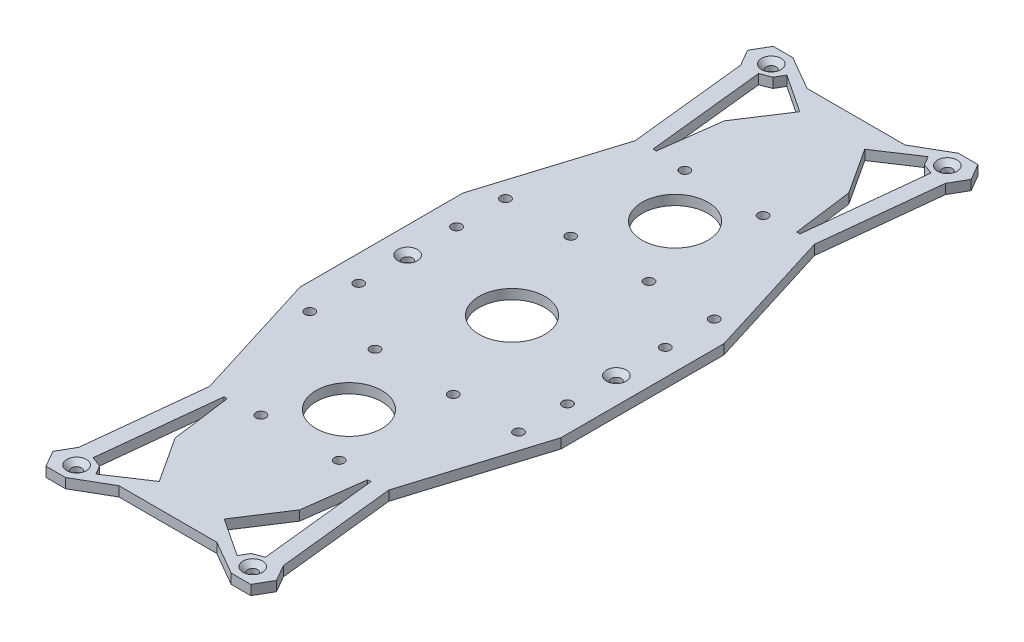
SolidWorks part; units mm, degrees
ref_plane "前视基准面" through (0, 0, 0) normal (0, 0, 1) x (1, 0, 0)
ref_plane "上视基准面" through (0, 0, 0) normal (0, 1, 0) x (1, 0, 0)
ref_plane "右视基准面" through (0, 0, 0) normal (1, 0, 0) x (0, 0, -1)
sketch "草图1" plane through (0, 0, 0) normal (0, 1, 0) x (1, 0, 0)
  line L0 (0, 0) -> (0, 105.5) construction
  line L1 (-15, 105.5) -> (15, 105.5)
  line L2 (-40, 25) -> (40, 25)
  line L3 (15, 105.5) -> (40, 25)
  line L4 (40, 25) -> (40, -25)
  line L5 (-40, 25) -> (-40, -25)
  line L6 (-15, 105.5) -> (-40, 25)
  line L7 (-40, 0) -> (49960, 0) construction
  line L8 (-15, -105.5) -> (15, -105.5)
  line L9 (15, -105.5) -> (40, -25)
  line L10 (-40, -25) -> (40, -25)
  line L11 (-15, -105.5) -> (-40, -25)
  point P9 (0, 25)
  point P14 (40, 0)
  point P15 (-40, 0)
extrude "凸台-拉伸1" add sketch "草图1" along normal blind 3 contours L11 L8 L9 L10 | L5 L10 L4 L2 | L1 L6 L2 L3
sketch "草图2" plane through (0, 3, 0) normal (0, 1, 0) x (1, 0, 0)
  line L0 (0, 0) -> (0, 50000) construction
  line L1 (-15, 105.5) -> (15, 105.5) construction
  line L2 (-40, 0) -> (49960, 0) construction
  line L3 (-40, 25) -> (-40, -25) construction
  line L4 (40, 25) -> (40, -25) construction
  point P5 (0, 105.5)
  point P10 (-40, 0)
  point P13 (40, 0)
sketch "草图3" plane through (0, 3, 0) normal (0, 1, 0) x (1, 0, 0)
  line L0 (0, 0) -> (0, 107.9436) construction
  line L1 (0, -200000) -> (0, 250000) construction
  line L2 (0, 0) -> (78.3198, 0) construction
  line L3 (-200040, 0) -> (249960, 0) construction
  circle A0 centre (3.5, 101.5) radius 1.5
  circle A1 centre (10, 89.5) radius 1.5
ref_plane "基准面1" through (0, 0, 0) normal (1, 0, 0) x (0, 0, -1)
ref_plane "基准面2" through (0, 0, 0) normal (0, 0, 1) x (1, 0, 0)
sketch "草图6" plane through (0, 3, 0) normal (0, 1, 0) x (1, 0, 0)
  circle A0 centre (27, 106.5) radius 3
sketch "草图7" plane through (0, 3, 0) normal (0, 1, 0) x (1, 0, 0)
  line L0 (15, 105.5) -> (25.3923, 111.5)
  line L1 (25.3923, 111.5) -> (31.3923, 111.5)
  line L2 (31.3923, 111.5) -> (34.2791, 106.5)
  line L3 (27, 106.5) -> (34.2791, 106.5) construction
  line L4 (31.3923, 101.5) -> (34.2791, 106.5)
  line L5 (31.3923, 101.5) -> (27.5, 65.25)
  line L6 (15, 105.5) -> (40, 25) construction
  line L7 (15, 105.5) -> (27.5, 65.25)
extrude "凸台-拉伸2" add sketch "草图7" against normal blind 3 contours L5 L7 L0 L1 L2 L4
sketch "草图8" plane through (0, 3, 0) normal (0, 1, 0) x (1, 0, 0)
  circle A0 centre (27, 106.5) radius 1.5
extrude "切除-拉伸4" cut sketch "草图8" against normal blind 3 contours A0
sketch "草图9" plane through (0, 3, 0) normal (0, 1, 0) x (1, 0, 0)
  line L0 (31.3923, 101.5) -> (26.4209, 102.0338)
  line L1 (26.4209, 102.0338) -> (22.2287, 62.9914)
  line L2 (27.5, 65.25) -> (22.5286, 65.7838)
  line L3 (26.4209, 102.0338) -> (23.2433, 103.2222)
  line L4 (23.2433, 103.2222) -> (21.6692, 105.9485)
  line L5 (21.6692, 105.9485) -> (16.6582, 102.628)
  line L6 (22.5286, 65.7838) -> (21.5286, 65.7838)
  line L7 (21.5286, 65.7838) -> (16.6582, 102.628)
  line L8 (16.6582, 102.628) -> (9.9707, 98.1967)
  line L9 (10.3134, 97.6711) -> (9.9707, 98.1967)
  line L10 (10.3134, 97.6711) -> (19.0934, 84.2059)
extrude "切除-拉伸6" cut sketch "草图9" against normal through all and the other way through all
sketch "草图13" plane through (0, 3, 0) normal (0, 1, 0) x (1, 0, 0)
  line L0 (-200040, 0) -> (249960, 0) construction
  circle A0 centre (32, 0) radius 1.5
hole_wizard "M3 六角凹锥坑螺钉的锥形沉头孔1" positions "草图11" profile "草图12" countersink size "M3" standard "ISO" end condition through all
sketch "草图11" plane through (0, 3, 0) normal (0, 1, 0) x (1, 0, 0)
  point P0 (27, 106.5)
  point P3 (32, 0)
sketch "草图12" plane through (27, 3, -106.5) normal (1, 0, 0) x (0, 0, 1)
  line L0 (0, 0) -> (0, 3)
  line L1 (0, 3) -> (1.5, 3)
  line L2 (1.5, 3) -> (1.5, 1.5)
  line L3 (1.5, 1.5) -> (3, 0)
  line L5 (3, 0) -> (0, 0)
  line L6 (-1.5, 1.5) -> (-3, 0) construction
  line L11 (0, -6.35) -> (0, 107.95) construction
  dimension "通孔孔直径" = 3
  dimension "通孔孔深度" = 3
  dimension "近端锥形沉头孔直径" = 6
  dimension "近端锥形沉头孔角度" = 90
mirror "镜向5" about plane through (0, 0, 0) normal (1, 0, 0) of "M3 六角凹锥坑螺钉的锥形沉头孔1"
mirror "镜向6" about plane through (0, 0, 0) normal (1, 0, 0) of "凸台-拉伸2", "切除-拉伸6", "M3 六角凹锥坑螺钉的锥形沉头孔1"
mirror "镜向7" about plane through (0, 0, 0) normal (0, 0, 1) of "镜向6", "凸台-拉伸2", "切除-拉伸6", "M3 六角凹锥坑螺钉的锥形沉头孔1"
sketch "草图14" plane through (0, 3, 0) normal (0, 1, 0) x (1, 0, 0)
  circle A0 centre (0, 0) radius 10.1
  circle A1 centre (0, -50) radius 10.1
  circle A2 centre (0, 0) radius 10.1
  circle A3 centre (0, 50) radius 10.1
  dimension "D1" = 2
  dimension "D2" = 2
extrude "切除-拉伸7" cut sketch "草图14" against normal through all contours A0 | A1 | A3
sketch "草图15" plane through (0, 0, 0) normal (0, -1, 0) x (1, 0, 0)
  line L0 (-32, 0) -> (-32, 50000) construction
  circle A0 centre (-32, 15) radius 1.5
  circle A1 centre (-32, 30) radius 1.5
  circle A2 centre (-12, 65) radius 1.5
  circle A3 centre (-12, 30) radius 1.5
  point P9 (0, 0)
extrude "切除-拉伸8" cut sketch "草图15" against normal blind 10
mirror "镜向8" about plane through (0, 0, 0) normal (1, 0, 0) of "切除-拉伸8"
mirror "镜向9" about plane through (0, 0, 0) normal (0, 0, 1) of "镜向8", "切除-拉伸8"
